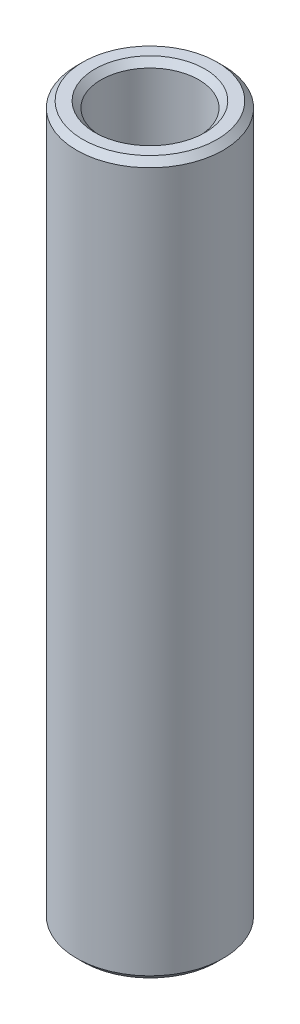
SolidWorks part; units mm, degrees
ref_plane "Front Plane" through (0, 0, 0) normal (0, 0, 1) x (1, 0, 0)
ref_plane "Top Plane" through (0, 0, 0) normal (0, 1, 0) x (1, 0, 0)
ref_plane "Right Plane" through (0, 0, 0) normal (1, 0, 0) x (0, 0, -1)
sketch "Sketch2" plane through (0, 0, 0) normal (0, 0, 1) x (1, 0, 0)
  line L0 (0, 9.9617) -> (0, -9.9617) construction
  line L1 (2, 14.5732) -> (2, -14.5732)
  line L2 (2, -14.5732) -> (3, -14.5732)
  line L3 (3, -14.5732) -> (3, 14.5732)
  line L4 (3, 14.5732) -> (2, 14.5732)
  point P6 (2, 0)
  dimension "D1" = 29.1465
  dimension "D2" = 6
  dimension "D3" = 4
revolve "Revolve1" add sketch "Sketch2" angle 360 about L0
chamfer "Chamfer2" distance 0.254 angle 45 4 edges at (-2, -14.5732, 0) (-3, -14.5732, 0) (-3, 14.5732, 0) (-2, 14.5732, 0)
